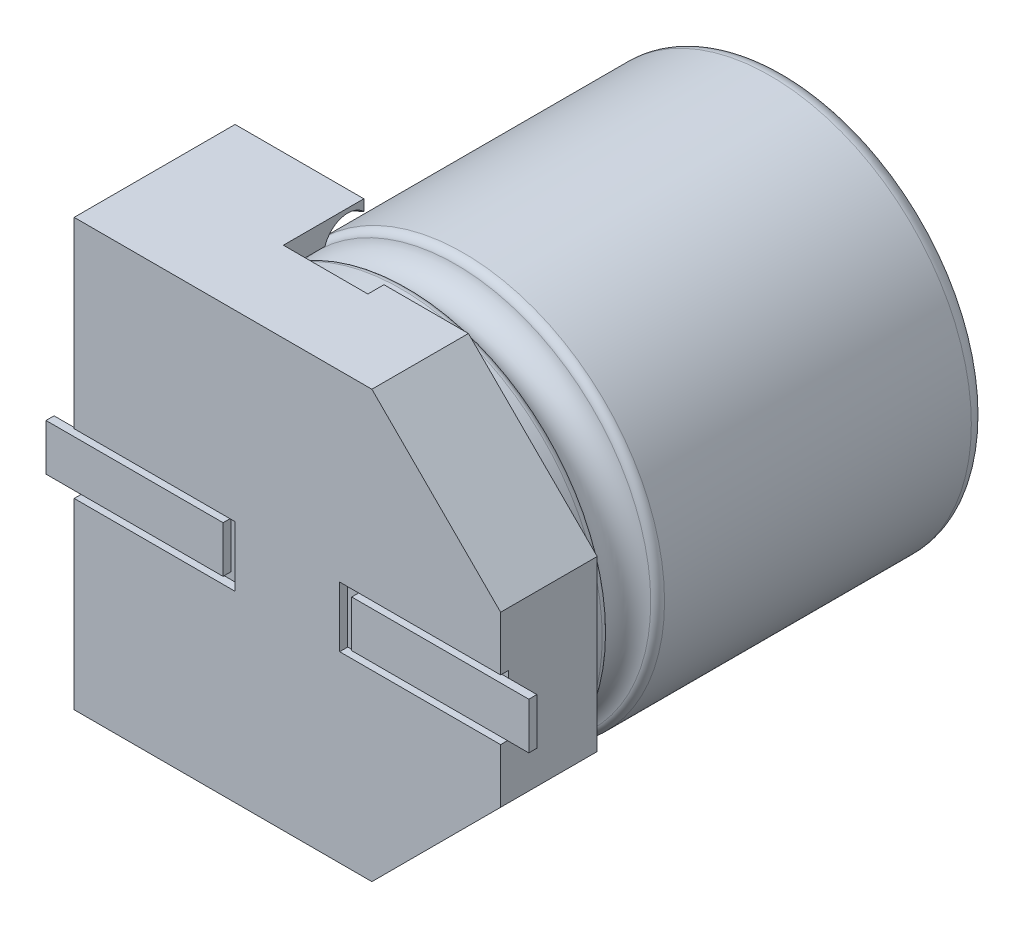
SolidWorks part; units mm, degrees
ref_plane "Front Plane" through (0, 0, 0) normal (0, 0, 1) x (1, 0, 0)
ref_plane "Top Plane" through (0, 0, 0) normal (0, 1, 0) x (1, 0, 0)
ref_plane "Right Plane" through (0, 0, 0) normal (1, 0, 0) x (0, 0, -1)
sketch "Szkic1" plane through (0, 0, 0) normal (0, 0, 1) x (1, 0, 0)
  line L0 (2.65, -1.05) -> (2.65, -0.375)
  line L1 (2.65, -0.375) -> (0.65, -0.375)
  line L2 (0.65, -0.375) -> (0.65, 0.375)
  line L3 (0.65, 0.375) -> (2.65, 0.375)
  line L4 (2.65, 0.375) -> (2.65, 1.05)
  line L5 (2.65, 1.05) -> (1.05, 2.65)
  line L6 (1.05, 2.65) -> (-2.65, 2.65)
  line L7 (-2.65, 2.65) -> (-2.65, 0.375)
  line L8 (-2.65, 0.375) -> (-0.65, 0.375)
  line L9 (-0.65, 0.375) -> (-0.65, -0.375)
  line L10 (-0.65, -0.375) -> (-2.65, -0.375)
  line L11 (-2.65, -0.375) -> (-2.65, -2.65)
  line L12 (-2.65, -2.65) -> (1.05, -2.65)
  line L13 (1.05, -2.65) -> (2.65, -1.05)
extrude "Dodanie-wyciągnięcie1" add sketch "Szkic1" along normal blind 2
sketch "Szkic2" plane through (0, 0, 0) normal (0, 0, -1) x (-1, 0, 0)
  line L0 (-2.65, 0.375) -> (-0.65, 0.375)
  line L1 (-0.65, 0.375) -> (-0.65, -0.375)
  line L2 (-0.65, -0.375) -> (-2.65, -0.375)
  line L3 (-2.65, -0.375) -> (-2.65, 0.375)
  line L4 (0.65, 0.375) -> (0.65, -0.375)
  line L5 (0.65, -0.375) -> (2.65, -0.375)
  line L6 (2.65, -0.375) -> (2.65, 0.375)
  line L7 (2.65, 0.375) -> (0.65, 0.375) construction
  line L8 (2.65, 0.375) -> (0.65, 0.375)
extrude "Dodanie-wyciągnięcie2" add sketch "Szkic2" against normal blind 1.9
sketch "Szkic3" plane through (0, 0, 1.9) normal (0, 0, 1) x (1, 0, 0)
  line L0 (0.65, 0) -> (-0.65, 0) construction
  line L1 (0.65, -0.375) -> (0.65, 0.375) construction
  line L2 (-0.65, 0.375) -> (-0.65, -0.375) construction
  line L3 (0, 0) -> (0, -0.9465) construction
  line L4 (3, 0.289) -> (0.7996, 0.289)
  line L5 (0.7996, 0.289) -> (0.7996, -0.289)
  line L6 (0.7996, -0.289) -> (3, -0.289)
  line L7 (3, -0.289) -> (3, 0.289)
  line L8 (2.65, -1.05) -> (2.65, -0.375) construction
  line L9 (-3, -0.289) -> (-3, 0.289)
  line L10 (-0.7996, -0.289) -> (-3, -0.289)
  line L11 (-0.7996, 0.289) -> (-0.7996, -0.289)
  line L12 (-3, 0.289) -> (-0.7996, 0.289)
  dimension "D1" = 0.35
extrude "Dodanie-wyciągnięcie3" add sketch "Szkic3" along normal blind 0.1 separate body
sketch "Szkic4" plane through (0, 0, 0) normal (0, 0, -1) x (-1, 0, 0)
  line L0 (1.05, 2.65) -> (0, 2.65)
  line L1 (0, 2.65) -> (0, 2.6)
  line L2 (0, -2.6) -> (0, -2.65)
  line L3 (0, -2.65) -> (1.05, -2.65)
  line L4 (1.05, -2.65) -> (1.05, -2.3785)
  line L5 (2.3785, -1.05) -> (2.65, -1.05)
  line L6 (2.65, -1.05) -> (2.65, 1.05)
  line L7 (2.65, 1.05) -> (2.3785, 1.05)
  line L8 (1.05, 2.3785) -> (1.05, 2.65)
  line L9 (2.65, 2.65) -> (2.65, -2.65) construction
  arc A0 (0, 2.6) -> (0, -2.6) centre (0, 0) ccw
  arc A1 (1.05, -2.3785) -> (2.3785, -1.05) centre (0, 0) ccw
  arc A2 (2.3785, 1.05) -> (1.05, 2.3785) centre (0, 0) ccw
  point P15 (2.65, 0)
  point P16 (2.65, 0)
extrude "Wytnij-wyciągnięcie1" cut sketch "Szkic4" against normal blind 1
sketch "Szkic5" plane through (0, 0, 0) normal (0, 0, -1) x (-1, 0, 0)
  line L0 (0.4947, 3.838) -> (0.4947, -3.9403)
  line L1 (0.4947, -3.9403) -> (-3.5992, -3.3262)
  line L2 (-3.5992, -3.3262) -> (-6.2261, 2.1322)
  line L3 (-6.2261, 2.1322) -> (0.4947, 3.838)
extrude "Wytnij-wyciągnięcie2" cut sketch "Szkic5" against normal blind 0.8
sketch "Szkic6" plane through (0, 0, 1) normal (0, 0, -1) x (-1, 0, 0)
  circle A0 centre (0, 0) radius 2.5
  dimension "D1" = 5
extrude "Dodanie-wyciągnięcie4" add sketch "Szkic6" along normal blind 5.2 separate body
fillet "Zaokrąglenie1" radius 0.2 1 edges at (-2.5, 0, -4.2)
sketch "Szkic7" plane through (0, 0, -4.2) normal (0, 0, -1) x (-1, 0, 0)
  line L0 (0.619, -2.2151) -> (0.6188, 2.2152)
  line L1 (0.6188, 2.2152) -> (0.619, -2.2151)
  circle A4 centre (0, 0) radius 2.3 construction
sketch "Szkic8" plane through (0, 0, -4.2) normal (0, 0, -1) x (-1, 0, 0)
  line L0 (-2.0064, -1.1245) -> (2.0064, -1.1245)
  line L1 (0, 0) -> (-2.3, 0) construction
  circle A0 centre (0, 0) radius 2.3 construction
  point P10 (-2.0064, -1.1245)
  point P11 (2.0064, -1.1245)
split line "Linia podziałowa4"
sketch "Szkic9" plane through (0, 0, 0) normal (0, 1, 0) x (1, 0, 0)
  line L0 (2.5, -1) -> (2.5, -0.2) construction
  line L1 (2.6, -1) -> (0, -1) construction
  line L2 (-2.5, -1) -> (2.5, -1) construction
  circle A0 centre (2.5, -0.2) radius 0.3
  dimension "D2" = 0.6
  dimension "D1" = 0.8
revolve "Wycięcie-obrót1" cut sketch "Szkic9" angle 360 about axis through (0, 0, -4.2) along (0, 0, 1)
fillet "Zaokrąglenie2" radius 0.1 2 edges at (-2.5, 0, 0.5) (2.5, 0, -0.1)
sketch "Szkic10" plane through (0, 0, -4.2) normal (0, 0, -1) x (-1, 0, 0)
  line L0 (-1.1, -1.1245) -> (-1.1, 1.5549) construction
  line L1 (2.0064, -1.1245) -> (-2.0064, -1.1245) construction
  line L2 (0, -1.1245) -> (0, 1.5549) construction
  line L3 (1.1, -1.1245) -> (1.1, 1.5549) construction
  text T0 "CS" font "Century Gothic" height 1
  text T1 "47" font "Century Gothic" height 1
  text T2 "25V" font "Century Gothic" height 1
  dimension "D1" = 1.1
  dimension "D2" = 1.1
split line "Linia podziałowa5"
